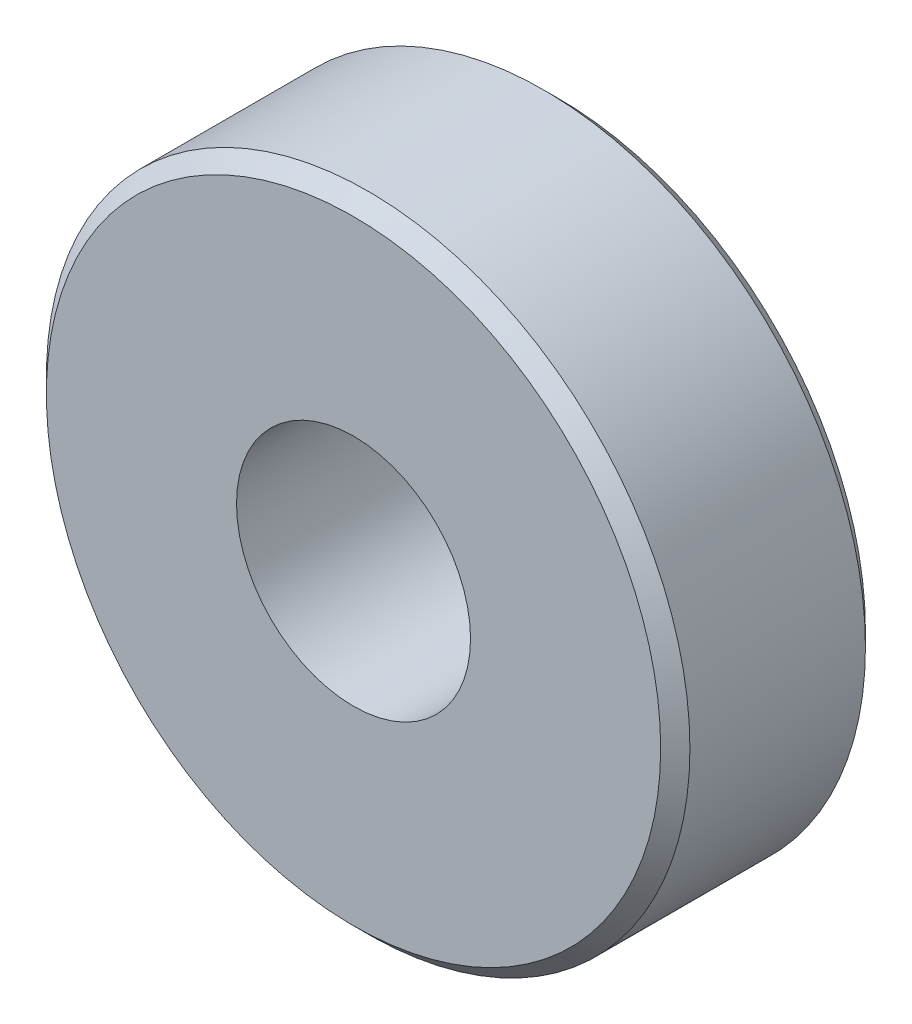
SolidWorks part; units mm, degrees
ref_plane "Plano frontal" through (0, 0, 0) normal (0, 0, 1) x (1, 0, 0)
ref_plane "Plano superior" through (0, 0, 0) normal (0, 1, 0) x (1, 0, 0)
ref_plane "Plano direito" through (0, 0, 0) normal (1, 0, 0) x (0, 0, -1)
sketch "Esboço1" plane through (0, 0, 0) normal (0, 0, 1) x (1, 0, 0)
  circle A0 centre (0, 0) radius 11
  circle A1 centre (0, 0) radius 4
extrude "Ressalto-extrusão1" add sketch "Esboço1" along normal blind 7
chamfer "Chanfro1" distance 0.5 angle 45 2 edges at (11, 0, 0) (11, 0, 7)
